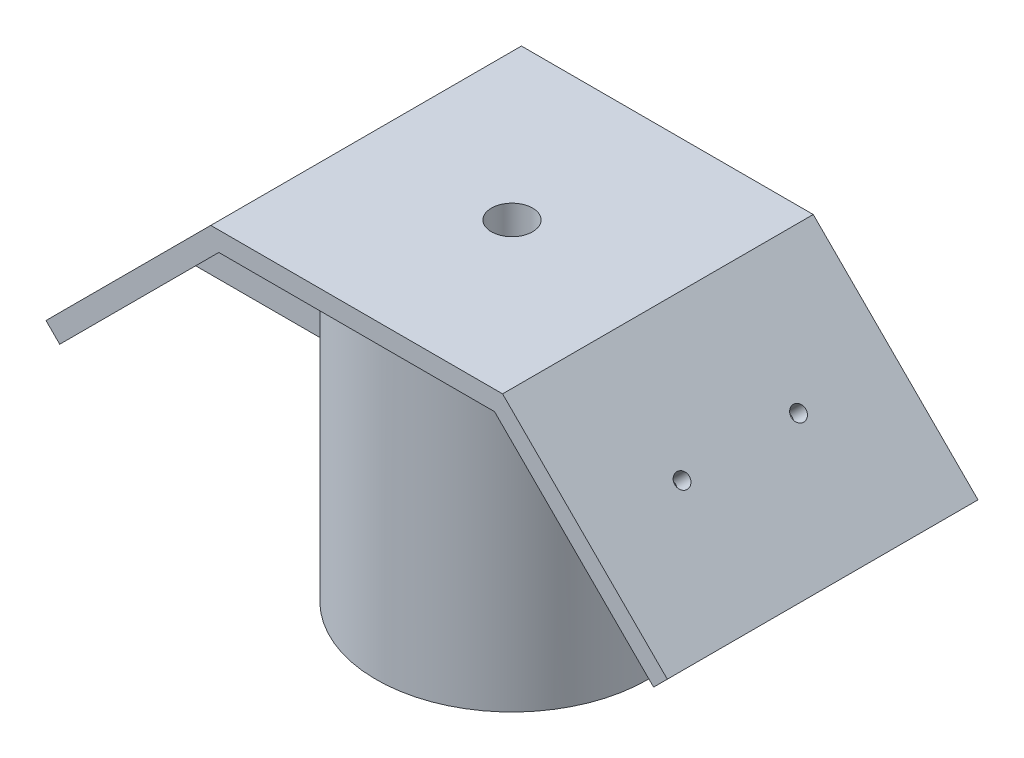
SolidWorks part; units mm, degrees
material "ABS"
ref_plane "Front Plane" through (0, 0, 0) normal (0, 0, 1) x (1, 0, 0)
ref_plane "Top Plane" through (0, 0, 0) normal (0, 1, 0) x (1, 0, 0)
ref_plane "Right Plane" through (0, 0, 0) normal (1, 0, 0) x (0, 0, -1)
sketch "Sketch1" plane through (0, 0, 0) normal (0, 0, 1) x (1, 0, 0)
  line L0 (-50.8, 0) -> (-50.8, 19.05) construction
  line L1 (-50.8, 0) -> (0, 0) construction
  line L2 (-50.8, 19.05) -> (-26.1043, 43.7457) construction
  line L3 (-26.1043, 43.7457) -> (-23.8592, 41.5006)
  line L4 (-23.8592, 41.5006) -> (-50.8, 14.5599) construction
  line L5 (0, 0) -> (0, 64.4396) construction
  line L6 (-50.8, 14.5599) -> (-23.8592, 41.5006)
  line L7 (-23.8592, 41.5006) -> (23.8592, 41.5006)
  line L8 (48.5549, 12.3148) -> (50.8, 14.5599)
  line L9 (22.5441, 38.3256) -> (-22.5441, 38.3256)
  line L10 (-22.5441, 38.3256) -> (-48.5549, 12.3148)
  line L11 (-50.8, 14.5599) -> (-48.5549, 12.3148)
  line L12 (22.5441, 38.3256) -> (48.5549, 12.3148)
  line L13 (50.8, 14.5599) -> (23.8592, 41.5006)
  circle A0 centre (-50.8, 0) radius 6.35 construction
  point P17 (0, 38.3256)
  point P18 (0, 41.5006)
  dimension "D2" = 12.7
  dimension "D1" = 50.8
  dimension "D3" = 19.05
  dimension "D4" = 135
  dimension "D5" = 3.175
  dimension "D6" = 38.1
  dimension "D7" = 3.175
  dimension "D8" = 3.175
  dimension "D9" = 38.1
extrude "Boss-Extrude1" add sketch "Sketch1" along normal blind 50.8
sketch "Sketch4" plane through (0, 38.3256, 0) normal (0, -1, 0) x (1, 0, 0)
  line L0 (0, 0) -> (0, 50.8) construction
  line L1 (22.5441, 0) -> (-22.5441, 0) construction
  line L2 (22.5441, 50.8) -> (-22.5441, 50.8) construction
  circle A0 centre (0, 25.4) radius 22.225
  point P6 (0, 25.4)
  dimension "D1" = 44.45
extrude "Boss-Extrude3" add sketch "Sketch4" along direction (0, -1, 0) on the side against the normal up to surface (50.8 mm away) from offset 50.8
sketch "Sketch8" plane through (-30.4349, 30.4349, 0) normal (0.7071, -0.7071, 0) x (0, 0, -1)
  line L0 (-50.8, -25.6256) -> (0, -25.6256) construction
  line L1 (-28.575, -25.6256) -> (-22.225, -25.6256)
  line L2 (-28.575, -25.6256) -> (-28.575, 11.1592)
  line L3 (-28.575, 11.1592) -> (-22.225, 11.1592)
  line L4 (-22.225, -25.6256) -> (-22.225, 11.1592)
  line L5 (-50.8, 11.1592) -> (0, 11.1592) construction
  point P8 (-25.4, -25.6256)
  dimension "D1" = 6.35
extrude "Boss-Extrude5" add sketch "Sketch8" along direction (1, 0, 0) on the side of the normal up to next (18.8437 mm away)
pattern_circular "CirPattern2" count 2 over 180 about axis through (0, 12.3148, 25.4) along (1, 0, 0) of "Boss-Extrude5"
sketch "Sketch9" plane through (0, 41.5006, 0) normal (0, 1, 0) x (1, 0, 0)
  line L0 (0, -50.8) -> (0, 0) construction
  line L1 (-23.8592, -50.8) -> (23.8592, -50.8) construction
  circle A0 centre (0, -25.4) radius 3.3655
  dimension "D1" = 6.731
extrude "Cut-Extrude1" cut sketch "Sketch9" against normal through all
sketch "Sketch10" plane through (-32.6799, 32.6799, 0) normal (-0.7071, 0.7071, 0) x (0, 0, 1)
  line L0 (0, -6.5756) -> (50.8, -6.5756) construction
  line L1 (0, -25.6256) -> (0, 12.4744) construction
  line L2 (50.8, -25.6256) -> (50.8, 12.4744) construction
  line L3 (25.4, -6.5756) -> (25.4, 12.4744) construction
  line L4 (50.8, 12.4744) -> (0, 12.4744) construction
  circle A0 centre (15.875, -6.5756) radius 1.1906
  circle A1 centre (34.925, -6.5756) radius 1.1906
  dimension "D2" = 2.3813
  dimension "D1" = 9.525
extrude "Cut-Extrude2" cut sketch "Sketch10" against normal up to next
mirror "Mirror2" about plane through (0, 0, 0) normal (1, 0, 0) of "Cut-Extrude2"
